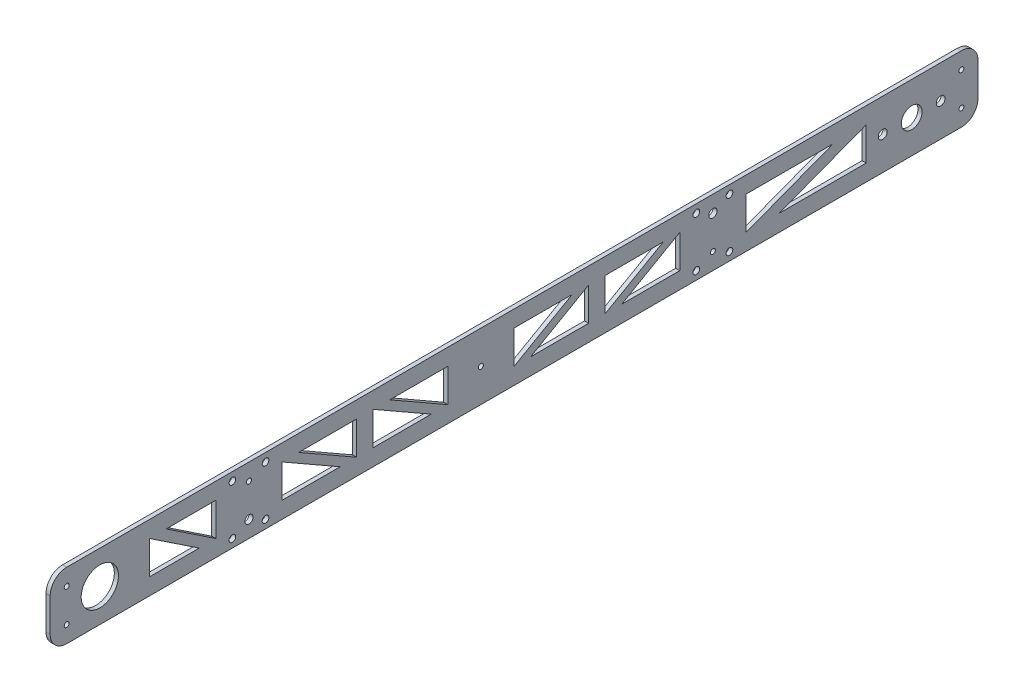
SolidWorks part; units mm, degrees
material "5052-H32"
ref_plane "Front Plane" through (0, 0, 0) normal (0, 0, 1) x (1, 0, 0)
ref_plane "Top Plane" through (0, 0, 0) normal (0, 1, 0) x (1, 0, 0)
ref_plane "Right Plane" through (0, 0, 0) normal (1, 0, 0) x (0, 0, -1)
sketch "Sketch1" plane through (0, 0, 0) normal (1, 0, 0) x (0, 0, -1)
  line L0 (-558.8, 50.8) -> (-558.8, 0) construction
  line L1 (-12.7, 0) -> (-698.5, 0)
  line L2 (0, 12.7) -> (0, 38.1)
  line L3 (-12.7, 50.8) -> (-698.5, 50.8)
  line L4 (-73.025, 25.4) -> (-28.575, 25.4) construction
  line L5 (-711.2, 38.1) -> (-711.2, 12.7)
  line L6 (-381, 105.6306) -> (-381, -44.8709) construction
  line L7 (-228.6, 38.1) -> (-228.6, 12.7)
  line L8 (-273.05, 12.7) -> (-228.6, 12.7)
  line L9 (-228.6, 38.1) -> (-273.05, 12.7)
  line L10 (-203.2, 57.15) -> (-203.2, 19.05) construction
  line L11 (-203.2, 12.7) -> (-558.8, 38.1) construction
  line L12 (-723.592, 38.1) -> (-635.8514, 38.1) construction
  line L13 (-644.5866, 12.7) -> (-579.0388, 12.7) construction
  line L14 (-635, 38.1) -> (-635, 12.7)
  line L15 (-635, 38.1) -> (-596.9, 12.7)
  line L16 (-596.9, 12.7) -> (-635, 12.7)
  line L17 (-622.3, 38.1) -> (-584.2, 38.1)
  line L18 (-584.2, 38.1) -> (-584.2, 12.7)
  line L19 (-584.2, 12.7) -> (-622.3, 38.1)
  line L20 (-533.4, 38.1) -> (-533.4, 12.7)
  line L21 (-533.4, 38.1) -> (-488.95, 12.7)
  line L22 (-488.95, 12.7) -> (-533.4, 12.7)
  line L23 (-406.4, 38.1) -> (-406.4, 12.7)
  line L24 (-406.4, 12.7) -> (-450.85, 38.1)
  line L25 (-450.85, 38.1) -> (-406.4, 38.1)
  line L26 (-419.1, 12.7) -> (-463.55, 38.1)
  line L27 (-463.55, 38.1) -> (-463.55, 12.7)
  line L28 (-463.55, 12.7) -> (-419.1, 12.7)
  line L29 (-476.25, 12.7) -> (-476.25, 38.1)
  line L30 (-476.25, 38.1) -> (-520.7, 38.1)
  line L31 (-520.7, 38.1) -> (-476.25, 12.7)
  line L32 (-241.3, 38.1) -> (-285.75, 12.7)
  line L33 (-285.75, 38.1) -> (-241.3, 38.1)
  line L34 (-285.75, 12.7) -> (-285.75, 38.1)
  line L35 (-298.45, 38.1) -> (-298.45, 12.7)
  line L36 (-298.45, 12.7) -> (-342.9, 12.7)
  line L37 (-342.9, 12.7) -> (-298.45, 38.1)
  line L38 (-355.6, 38.1) -> (-355.6, 12.7)
  line L39 (-355.6, 12.7) -> (-311.15, 38.1)
  line L40 (-311.15, 38.1) -> (-355.6, 38.1)
  line L47 (-177.8, 38.1) -> (-177.8, 12.7)
  line L48 (-177.8, 12.7) -> (-111.125, 38.1)
  line L49 (-111.125, 38.1) -> (-177.8, 38.1)
  line L50 (-85.725, 38.1) -> (-85.725, 12.7)
  line L51 (-85.725, 12.7) -> (-152.4, 12.7)
  line L52 (-152.4, 12.7) -> (-85.725, 38.1)
  line L53 (-215.9, 44.45) -> (-215.9, 6.35) construction
  line L54 (-215.9, 44.45) -> (-190.5, 44.45) construction
  line L55 (-190.5, 44.45) -> (-190.5, 6.35) construction
  line L56 (-190.5, 6.35) -> (-215.9, 6.35) construction
  line L57 (-571.5, 44.45) -> (-571.5, 6.35) construction
  line L58 (-571.5, 6.35) -> (-546.1, 6.35) construction
  line L59 (-546.1, 6.35) -> (-546.1, 44.45) construction
  line L60 (-546.1, 44.45) -> (-571.5, 44.45) construction
  circle A0 centre (-50.8, 25.4) radius 7.9629
  circle A1 centre (-28.575, 25.4) radius 3.3782
  circle A2 centre (-215.9, 44.45) radius 2.5527
  circle A3 centre (-190.5, 44.45) radius 2.5527
  circle A4 centre (-190.5, 6.35) radius 2.5527
  circle A5 centre (-215.9, 6.35) radius 2.5527
  circle A6 centre (-73.025, 25.4) radius 3.3782
  circle A7 centre (-673.1, 25.4) radius 14.2875
  arc A8 (0, 12.7) -> (-12.7, 0) centre (-12.7, 12.7) cw
  arc A9 (0, 38.1) -> (-12.7, 50.8) centre (-12.7, 38.1) ccw
  arc A10 (-711.2, 38.1) -> (-698.5, 50.8) centre (-698.5, 38.1) cw
  arc A11 (-698.5, 0) -> (-711.2, 12.7) centre (-698.5, 12.7) cw
  circle A12 centre (-571.5, 44.45) radius 2.5527
  circle A13 centre (-546.1, 44.45) radius 2.5527
  circle A14 centre (-12.7, 38.1) radius 1.8986
  circle A15 centre (-12.7, 12.7) radius 1.8986
  circle A16 centre (-546.1, 6.35) radius 2.5527
  circle A17 centre (-571.5, 6.35) radius 2.5527
  circle A18 centre (-558.8, 12.7) radius 3.1496
  circle A19 centre (-203.2, 38.1) radius 3.175
  circle A20 centre (-698.5, 38.1) radius 1.8986
  circle A21 centre (-698.5, 12.7) radius 1.8986
  circle A22 centre (-558.8, 38.1) radius 1.8986
  circle A23 centre (-203.2, 12.7) radius 1.8987
  circle A24 centre (-381, 25.4) radius 1.8987
  point P13 (-50.8, 25.4)
  point P17 (0, 0)
  point P20 (0, 50.8)
  point P33 (-711.2, 50.8)
  point P37 (-381, 25.4)
  point P58 (-381, 25.4)
  point P77 (-381, 25.4)
  dimension "D7" = 28.575
  dimension "D8" = 3.7973
  dimension "D9" = 50.8
  dimension "D10" = 12.7
  dimension "D11" = 12.7
  dimension "D22" = 12.7
  dimension "D25" = 12.7
  dimension "D26" = 25.4
  dimension "D23" = 6.7564
  dimension "D24" = 44.45
  dimension "D27" = 12.7
  dimension "D33" = 12.7
  dimension "D34" = 6.35
  dimension "D35" = 12.7
  dimension "D37" = 3.7973
  dimension "D38" = 3.7973
  dimension "D39" = 3.7973
  dimension "D46" = 12.7
  dimension "D47" = 12.7
  dimension "D48" = 12.7
  dimension "D13" = 25.4
  dimension "D15" = 12.7
  dimension "D16" = 12.7
  dimension "D17" = 25.4
  dimension "D19" = 15.9258
  dimension "D5" = 6.7564
  dimension "D32" = 6.2992
  dimension "D4" = 3.7973
  dimension "D41" = 3.7973
  dimension "D43" = 3.7973
  dimension "D12" = 38.1
  dimension "D55" = 5.1054
  dimension "D56" = 5.1054
  dimension "D57" = 5.1054
  dimension "D58" = 5.1054
  dimension "D63" = 5.1054
  dimension "D64" = 5.1054
  dimension "D65" = 5.1054
  dimension "D66" = 5.1054
  dimension "D2" = 50.8
  dimension "D6" = 25.4
  dimension "D14" = 711.2
  dimension "D18" = 558.8
  dimension "D20" = 25.4
  dimension "D21" = 38.1
  dimension "D29" = 25.4
  dimension "D30" = 25.4
  dimension "D31" = 203.2
  dimension "D40" = 12.7
  dimension "D42" = 12.7
  dimension "D44" = 25.4
  dimension "D45" = 12.7
  dimension "D49" = 12.7
  dimension "D50" = 82.55
  dimension "D51" = 6.35
  dimension "D52" = 6.35
  dimension "D53" = 12.7
  dimension "D59" = 6.35
  dimension "D60" = 6.35
  dimension "D61" = 12.7
  dimension "D62" = 12.7
extrude "Boss-Extrude1" add sketch "Sketch1" along normal blind 3.175
